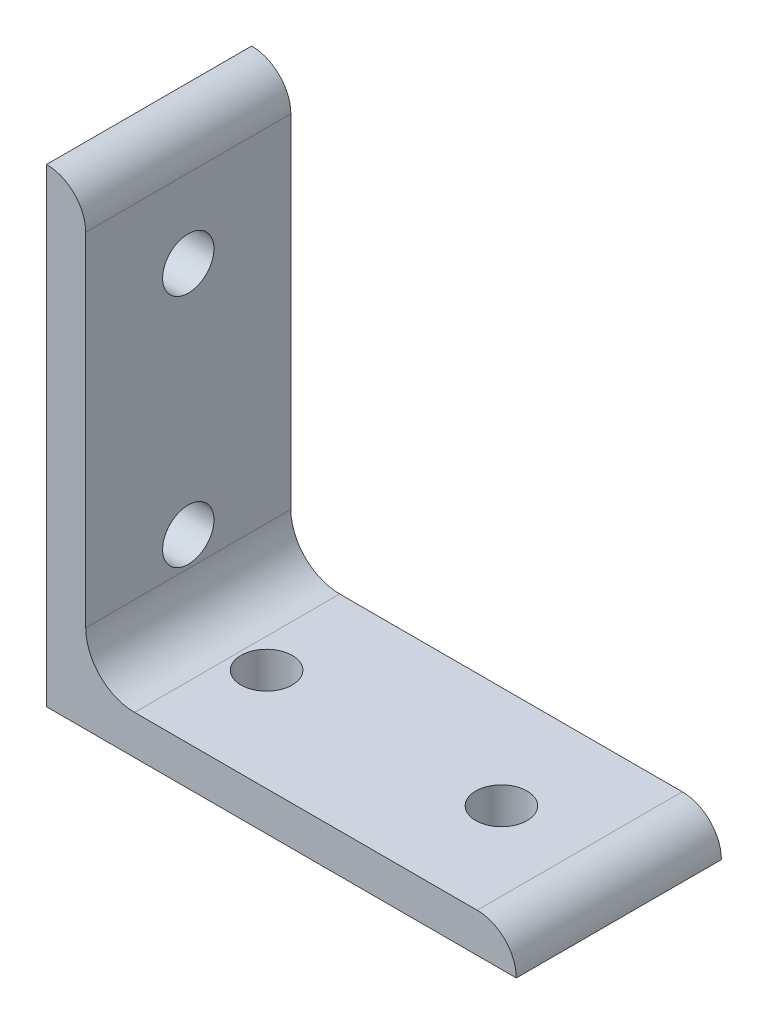
SolidWorks part; units mm, degrees
ref_plane "Front Plane" through (0, 0, 0) normal (0, 0, 1) x (1, 0, 0)
ref_plane "Top Plane" through (0, 0, 0) normal (0, 1, 0) x (1, 0, 0)
ref_plane "Right Plane" through (0, 0, 0) normal (1, 0, 0) x (0, 0, -1)
sketch "Sketch1" plane through (0, 0, 0) normal (0, 0, 1) x (1, 0, 0)
  line L0 (0, 0) -> (0, 76.2)
  line L1 (6.35, 69.85) -> (6.35, 76.2) construction
  line L2 (6.35, 69.85) -> (6.35, 14.2748)
  line L3 (14.2748, 6.35) -> (69.85, 6.35)
  line L4 (6.35, 76.2) -> (0, 76.2) construction
  line L5 (76.2, 0) -> (0, 0)
  line L6 (69.85, 6.35) -> (76.2, 6.35) construction
  line L7 (76.2, 6.35) -> (76.2, 0) construction
  arc A0 (6.35, 69.85) -> (0, 76.2) centre (0, 69.85) ccw
  arc A1 (76.2, 0) -> (69.85, 6.35) centre (69.85, 0) ccw
  arc A2 (6.35, 14.2748) -> (14.2748, 6.35) centre (14.2748, 14.2748) ccw
  point P10 (6.35, 73.025)
  dimension "E" = 7.9248
  dimension "D" = 6.35
  dimension "C" = 76.2
  dimension "B" = 76.2
extrude "Boss-Extrude1" add sketch "Sketch1" along normal mid plane 33.274
sketch "Sketch2" plane through (0, 0, 0) normal (0, 1, 0) x (1, 0, 0)
  line L0 (0, 0) -> (19.05, 0) construction
  line L1 (19.05, 0) -> (57.15, 0) construction
  circle A0 centre (19.05, 0) radius 4.1656
  circle A1 centre (57.15, 0) radius 4.1656
extrude "Cut-Extrude1" cut sketch "Sketch2" along normal through all
sketch "Sketch3" plane through (0, 0, 0) normal (1, 0, 0) x (0, 0, -1)
  line L0 (0, 0) -> (0, 19.05) construction
  line L1 (0, 19.05) -> (0, 57.15) construction
  circle A0 centre (0, 19.05) radius 4.1656
  circle A1 centre (0, 57.15) radius 4.1656
  dimension "D1" = 19.05
  dimension "D2" = 38.1
extrude "Cut-Extrude2" cut sketch "Sketch3" along normal through all
equation "\"E@Sketch3\" = \"E@Sketch2\""
equation "\"D1@Sketch3\" = \"D1@Sketch2\""
equation "\"D2@Sketch3\" = \"D2@Sketch2\""
